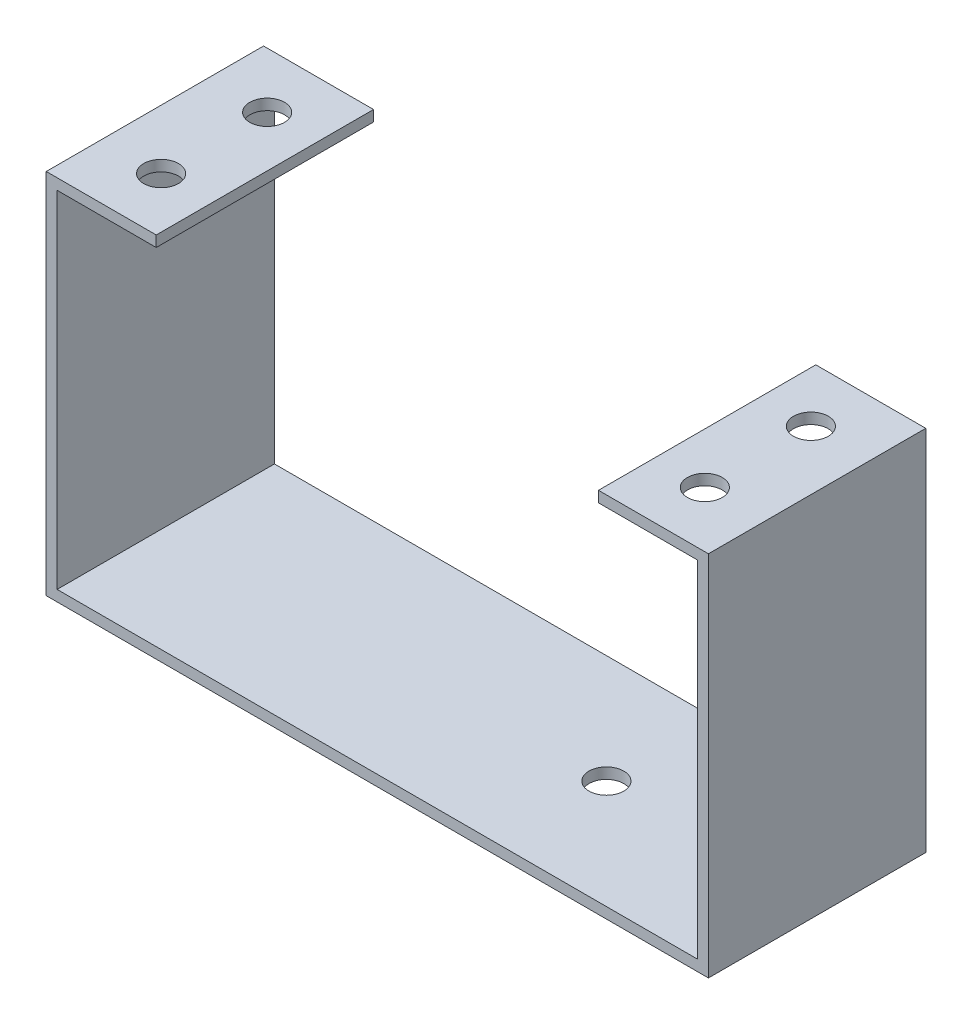
SolidWorks part; units mm, degrees
ref_plane "正面" through (0, 0, 0) normal (0, 0, 1) x (1, 0, 0)
ref_plane "平面" through (0, 0, 0) normal (0, 1, 0) x (1, 0, 0)
ref_plane "右側面" through (0, 0, 0) normal (1, 0, 0) x (0, 0, -1)
sketch "ｽｹｯﾁ2" plane through (0, 0, 0) normal (0, 1, 0) x (1, 0, 0)
  line L1 (0, 0) -> (60.94, 0)
  line L2 (0, 0) -> (0, 20)
  line L3 (0, 20) -> (60.94, 20)
  line L4 (60.94, 0) -> (60.94, 20)
extrude "ﾎﾞｽ - 押し出し1" add sketch "ｽｹｯﾁ2" along normal blind 1
sketch "ｽｹｯﾁ3" plane through (0, 1, 0) normal (0, 1, 0) x (1, 0, 0)
  line L0 (0, 0) -> (60.94, 0) construction
  line L1 (60.94, 20) -> (59.94, 20)
  line L2 (60.94, 20) -> (60.94, 0)
  line L3 (60.94, 0) -> (59.94, 0)
  line L4 (59.94, 20) -> (59.94, 0)
extrude "ﾎﾞｽ - 押し出し2" add sketch "ｽｹｯﾁ3" along normal blind 32.81
sketch "ｽｹｯﾁ4" plane through (0, 1, 0) normal (0, 1, 0) x (1, 0, 0)
  line L0 (0, 0) -> (59.94, 0) construction
  line L1 (0, 20) -> (1, 20)
  line L2 (0, 20) -> (0, 0)
  line L3 (0, 0) -> (1, 0)
  line L4 (1, 20) -> (1, 0)
extrude "ﾎﾞｽ - 押し出し3" add sketch "ｽｹｯﾁ4" along normal blind 32.81
sketch "ｽｹｯﾁ9" plane through (59.94, 0, 0) normal (-1, 0, 0) x (0, 0, 1)
  line L0 (0, 33.81) -> (0, 1) construction
  line L1 (-20, 33.81) -> (0, 33.81)
  line L2 (-20, 33.81) -> (-20, 32.81)
  line L3 (-20, 32.81) -> (0, 32.81)
  line L4 (0, 33.81) -> (0, 32.81)
extrude "ﾎﾞｽ - 押し出し8" add sketch "ｽｹｯﾁ9" along normal blind 9.12
sketch "ｽｹｯﾁ10" plane through (1, 0, 0) normal (1, 0, 0) x (0, 0, -1)
  line L0 (20, 33.81) -> (20, 1) construction
  line L1 (0, 33.81) -> (20, 33.81)
  line L2 (0, 33.81) -> (0, 32.81)
  line L3 (0, 32.81) -> (20, 32.81)
  line L4 (20, 33.81) -> (20, 32.81)
extrude "ﾎﾞｽ - 押し出し9" add sketch "ｽｹｯﾁ10" along normal blind 9.12
sketch "ｽｹｯﾁ13" plane through (0, 33.81, 0) normal (0, 1, 0) x (1, 0, 0)
  circle A0 centre (55.49, 5.12) radius 1.6
extrude "ｶｯﾄ - 押し出し2" cut sketch "ｽｹｯﾁ13" against normal blind 1
sketch "ｽｹｯﾁ14" plane through (0, 33.81, 0) normal (0, 1, 0) x (1, 0, 0)
  circle A0 centre (55.49, 14.88) radius 1.6
extrude "ｶｯﾄ - 押し出し3" cut sketch "ｽｹｯﾁ14" against normal blind 1
sketch "ｽｹｯﾁ15" plane through (0, 33.81, 0) normal (0, 1, 0) x (1, 0, 0)
  circle A0 centre (5.45, 5.12) radius 1.6
extrude "ｶｯﾄ - 押し出し4" cut sketch "ｽｹｯﾁ15" against normal blind 1
sketch "ｽｹｯﾁ16" plane through (0, 33.81, 0) normal (0, 1, 0) x (1, 0, 0)
  circle A0 centre (5.45, 14.88) radius 1.6
extrude "ｶｯﾄ - 押し出し5" cut sketch "ｽｹｯﾁ16" against normal blind 1
sketch "ｽｹｯﾁ17" plane through (0, 0, 0) normal (0, -1, 0) x (-1, 0, 0)
  circle A0 centre (-41.55, 10) radius 1.6
extrude "ｶｯﾄ - 押し出し6" cut sketch "ｽｹｯﾁ17" against normal blind 1 contours A0
